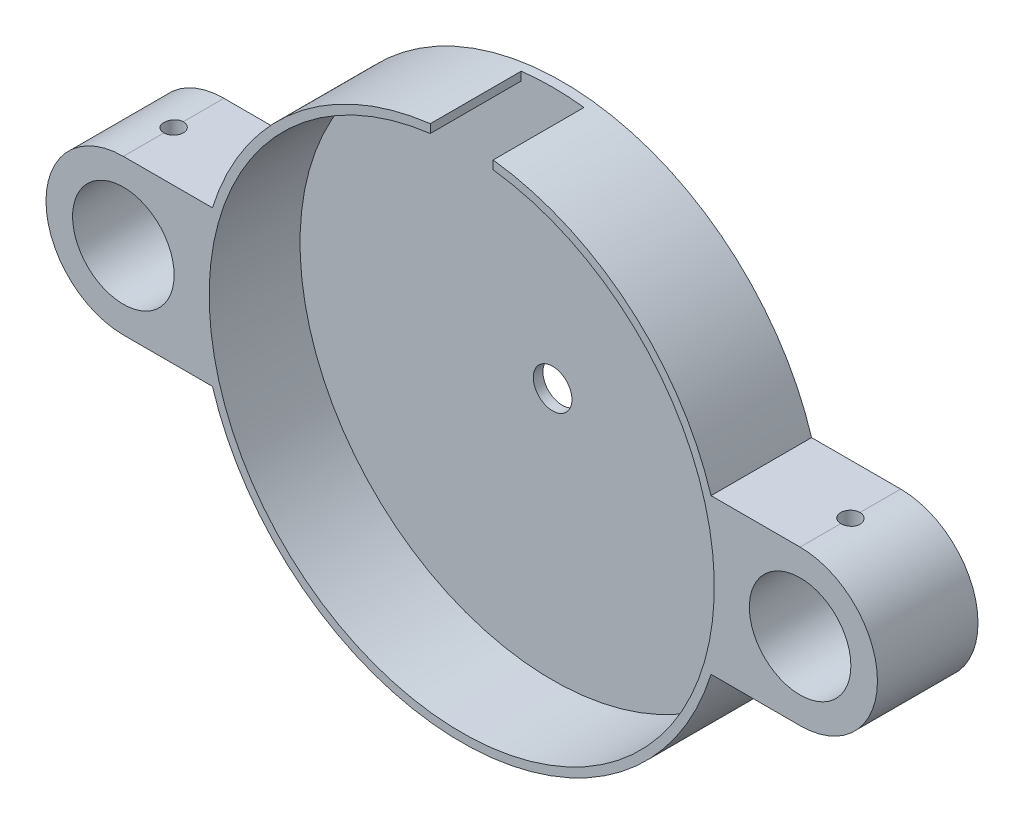
SolidWorks part; units mm, degrees
ref_plane "Front Plane" through (0, 0, 0) normal (0, 0, 1) x (1, 0, 0)
ref_plane "Top Plane" through (0, 0, 0) normal (0, 1, 0) x (1, 0, 0)
ref_plane "Right Plane" through (0, 0, 0) normal (1, 0, 0) x (0, 0, -1)
sketch "Sketch1" plane through (0, 0, 0) normal (0, 0, 1) x (1, 0, 0)
  circle A0 centre (0, 0) radius 54
  dimension "D1" = 108
extrude "Boss-Extrude1" add sketch "Sketch1" along normal blind 20.8 contours A0
sketch "Sketch2" plane through (0, 0, 0) normal (0, 0, 1) x (1, 0, 0)
  circle A0 centre (0, 0) radius 52.25
  dimension "D1" = 104.5
extrude "Cut-Extrude2" cut sketch "Sketch2" along normal up to surface (18.8 mm away) from offset 2 up to face at (54, 0, 20.8)
sketch "Sketch3" plane through (0, 0, 0) normal (0, 0, 1) x (1, 0, 0)
  line L0 (-70, 16) -> (-51.5752, 16)
  line L1 (-70, -16) -> (-51.5752, -16)
  line L2 (70, 16) -> (51.5752, 16)
  line L3 (70, -16) -> (51.5752, -16)
  circle A0 centre (70, 0) radius 10.5
  circle A1 centre (-70, 0) radius 10.5
  arc A2 (-70, 16) -> (-70, -16) centre (-70, 0) ccw
  circle A3 centre (0, 0) radius 54 construction
  arc A4 (70, -16) -> (70, 16) centre (70, 0) ccw
  arc A5 (51.5752, 16) -> (51.5752, -16) centre (0, 0) cw
  arc A6 (-51.5752, 16) -> (-51.5752, -16) centre (0, 0) ccw
  dimension "D1" = 21
  dimension "D2" = 70
extrude "Boss-Extrude2" add sketch "Sketch3" along normal up to surface (20.8 mm away) contours A6 L0 A2 L1 A1 | L2 A5 L3 A4 A0 up to face at (52.25, 0, 20.8)
sketch "Sketch4" plane through (0, 0, 0) normal (0, 0, 1) x (1, 0, 0)
  circle A0 centre (0, 0) radius 4
  dimension "D1" = 8
extrude "Cut-Extrude3" cut sketch "Sketch4" along normal up to surface (2 mm away) contours A0 up to face at (52.25, 0, 2)
sketch "Sketch5" plane through (0, 0, 0) normal (0, 0, 1) x (1, 0, 0)
  line L1 (-6.5, 0) -> (6.5, 0)
  line L2 (-6.5, 0) -> (-6.5, 59.7592)
  line L3 (-6.5, 59.7592) -> (6.5, 59.7592)
  line L4 (6.5, 0) -> (6.5, 59.7592)
  dimension "D1" = 13
extrude "Cut-Extrude4" cut sketch "Sketch5" along normal up to surface (18.8 mm away) from offset 2 up to face at (52.25, 0, 20.8)
sketch "Sketch6" plane through (0, 0, 0) normal (0, 1, 0) x (1, 0, 0)
  line L0 (-70, -20.8) -> (-70, 0) construction
  line L1 (70, -20.8) -> (70, 0) construction
  circle A0 centre (-70, -10.4) radius 2
  circle A1 centre (70, -10.4) radius 2
  point P7 (-70, -10.4)
  point P10 (70, -10.4)
  dimension "D1" = 4
  dimension "D2" = 140
extrude "Cut-Extrude5" cut sketch "Sketch6" along normal up to surface (16 mm away) up to face at (-60.7876, 16, 10.4)
